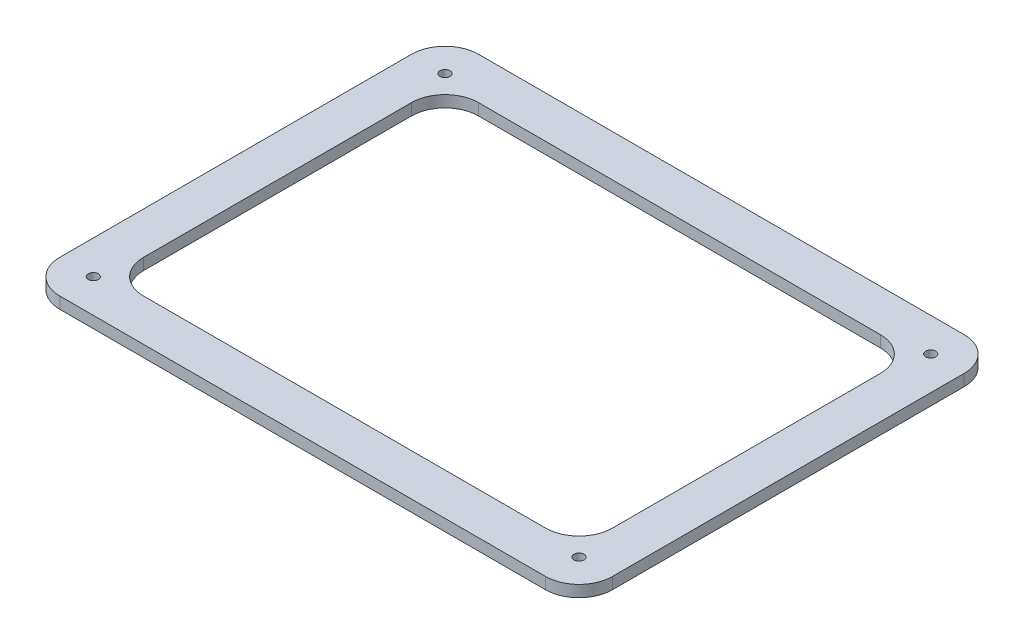
SolidWorks part; units mm, degrees
material "Delrin 2700 NC010, Low Viscosity Acetal Copolymer (SS)"
ref_plane "Front Plane" through (0, 0, 0) normal (0, 0, 1) x (1, 0, 0)
ref_plane "Top Plane" through (0, 0, 0) normal (0, 1, 0) x (1, 0, 0)
ref_plane "Right Plane" through (0, 0, 0) normal (1, 0, 0) x (0, 0, -1)
sketch "Sketch1" plane through (0, 0, 0) normal (0, 1, 0) x (1, 0, 0)
  line L0 (165, 125) -> (-165, -125) construction
  line L5 (-165, -125) -> (165, -125)
  line L6 (-165, -125) -> (-165, 125)
  line L7 (-165, 125) -> (165, 125)
  line L8 (165, -125) -> (165, 125)
  point P5 (0, 0)
  dimension "D1" = 330
  dimension "D2" = 250
extrude "Boss-Extrude1" add sketch "Sketch1" along normal blind 6.9
sketch "Sketch2" plane through (0, 6.9, 0) normal (0, 1, 0) x (1, 0, 0)
  line L0 (145, 105) -> (-145, -105) construction
  line L1 (-145, 105) -> (145, 105) construction
  line L2 (-145, 105) -> (-145, -105) construction
  line L3 (-145, -105) -> (145, -105) construction
  line L4 (145, 105) -> (145, -105) construction
  line L5 (0, 105) -> (0, 125) construction
  line L6 (165, 125) -> (-165, 125) construction
  line L8 (-145, 0) -> (-165, 0) construction
  line L9 (-165, 125) -> (-165, -125) construction
  circle A0 centre (-145, 105) radius 3
  circle A1 centre (145, 105) radius 3
  circle A2 centre (145, -105) radius 3
  circle A3 centre (-145, -105) radius 3
  point P4 (0, 0)
  dimension "D2" = 6
  dimension "D1" = 20
extrude "Cut-Extrude1" cut sketch "Sketch2" against normal through all
sketch "Sketch3" plane through (0, 6.9, 0) normal (0, 1, 0) x (1, 0, 0)
  line L0 (140, 100) -> (-140, -100) construction
  line L1 (-140, 100) -> (140, 100)
  line L2 (-140, 100) -> (-140, -100)
  line L3 (-140, -100) -> (140, -100)
  line L4 (140, 100) -> (140, -100)
  line L5 (0, 125) -> (0, 100) construction
  line L6 (165, 125) -> (-165, 125) construction
  line L8 (-140, 0) -> (-165, 0) construction
  line L9 (-165, 125) -> (-165, -125) construction
  point P4 (0, 0)
  dimension "D1" = 25
extrude "Cut-Extrude2" cut sketch "Sketch3" against normal through all
fillet "Fillet1" radius 20 4 edges at (165, 3.45, -125) (-165, 3.45, -125) (-165, 3.45, 125) (165, 3.45, 125)
fillet "Fillet2" radius 20 4 edges at (-140, 3.45, 100) (140, 3.45, 100) (140, 3.45, -100) (-140, 3.45, -100)
